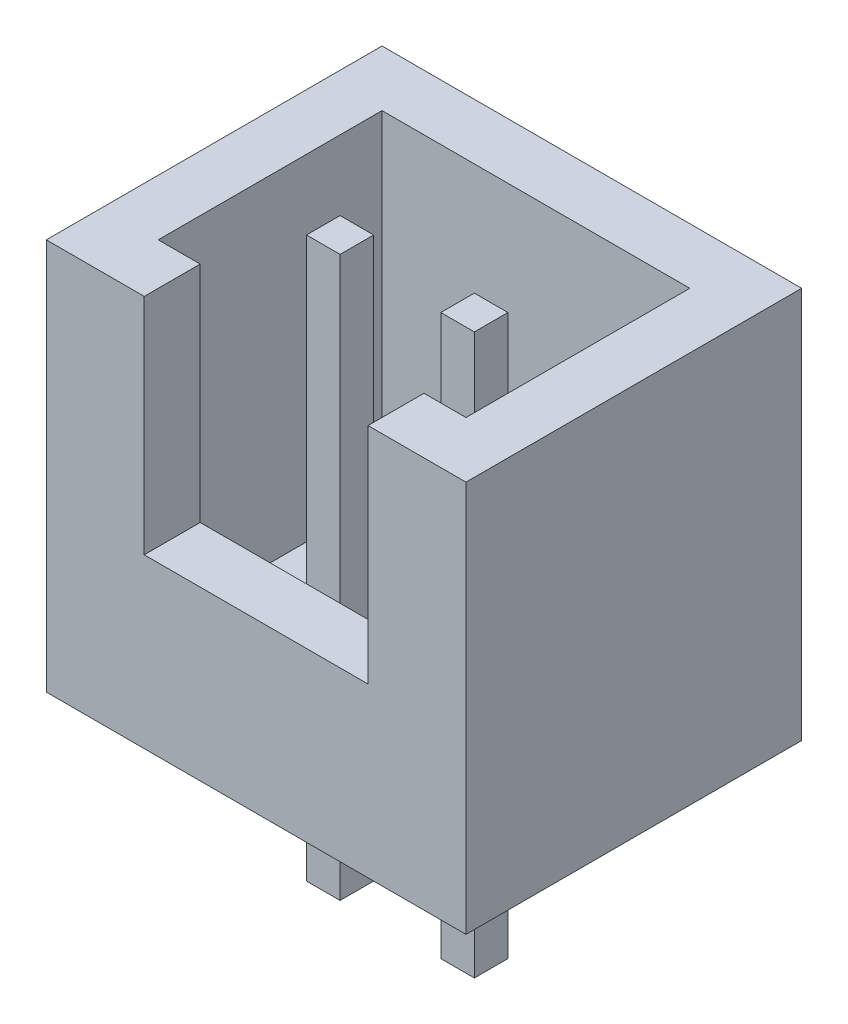
SolidWorks part; units mm, degrees
ref_plane "前视基准面" through (0, 0, 0) normal (0, 0, 1) x (1, 0, 0)
ref_plane "上视基准面" through (0, 0, 0) normal (0, 1, 0) x (1, 0, 0)
ref_plane "右视基准面" through (0, 0, 0) normal (1, 0, 0) x (0, 0, -1)
sketch "草图1" plane through (0, 0, 0) normal (0, 1, 0) x (1, 0, 0)
  line L1 (-3.75, 3) -> (3.75, 3)
  line L2 (-3.75, 3) -> (-3.75, -3)
  line L3 (-3.75, -3) -> (3.75, -3)
  line L4 (3.75, 3) -> (3.75, -3)
  line L5 (-3.75, 3) -> (3.75, -3) construction
  line L6 (-3.75, -3) -> (3.75, 3) construction
  point P0 (0, 0)
  dimension "D1" = 6
  dimension "D2" = 7.5
extrude "凸台-拉伸1" add sketch "草图1" along normal blind 7
shell "抽壳1" thickness 1
sketch "草图2" plane through (0, 0, 3) normal (0, 0, 1) x (1, 0, 0)
  line L0 (-3.75, 7) -> (3.75, 7) construction
  line L1 (-2, 7) -> (2, 7)
  line L2 (-2, 7) -> (-2, 3)
  line L3 (-2, 3) -> (2, 3)
  line L4 (2, 7) -> (2, 3)
  line L5 (0, 0) -> (0, 7) construction
  dimension "D1" = 4
  dimension "D2" = 4
extrude "切除-拉伸1" cut sketch "草图2" against normal up to next
sketch "草图3" plane through (0, 0, 0) normal (0, -1, 0) x (1, 0, 0)
  line L0 (0, 0) -> (0, 3) construction
  line L1 (-1.5, 0.6) -> (-0.9, 0.6)
  line L2 (-1.5, 0.6) -> (-1.5, 0)
  line L3 (-1.5, 0) -> (-0.9, 0)
  line L4 (-0.9, 0.6) -> (-0.9, 0)
  line L5 (-1.5, 0.6) -> (-0.9, 0) construction
  line L6 (-1.5, 0) -> (-0.9, 0.6) construction
  line L7 (-3.75, 3) -> (3.75, 3) construction
  line L8 (1.5, 0) -> (0.9, 0.6) construction
  line L9 (1.5, 0.6) -> (0.9, 0) construction
  line L10 (0.9, 0.6) -> (0.9, 0)
  line L11 (1.5, 0) -> (0.9, 0)
  line L12 (1.5, 0.6) -> (1.5, 0)
  line L13 (1.5, 0.6) -> (0.9, 0.6)
  point P0 (-1.2, 0.3)
  point P14 (1.2, 0.3)
  dimension "D1" = 0.6
  dimension "D2" = 0.6
  dimension "D3" = 3
  dimension "D4" = 3
extrude "凸台-拉伸2" add sketch "草图3" along normal blind 10 from surface at -7 starting at face at (0, 7, 0.8333)
